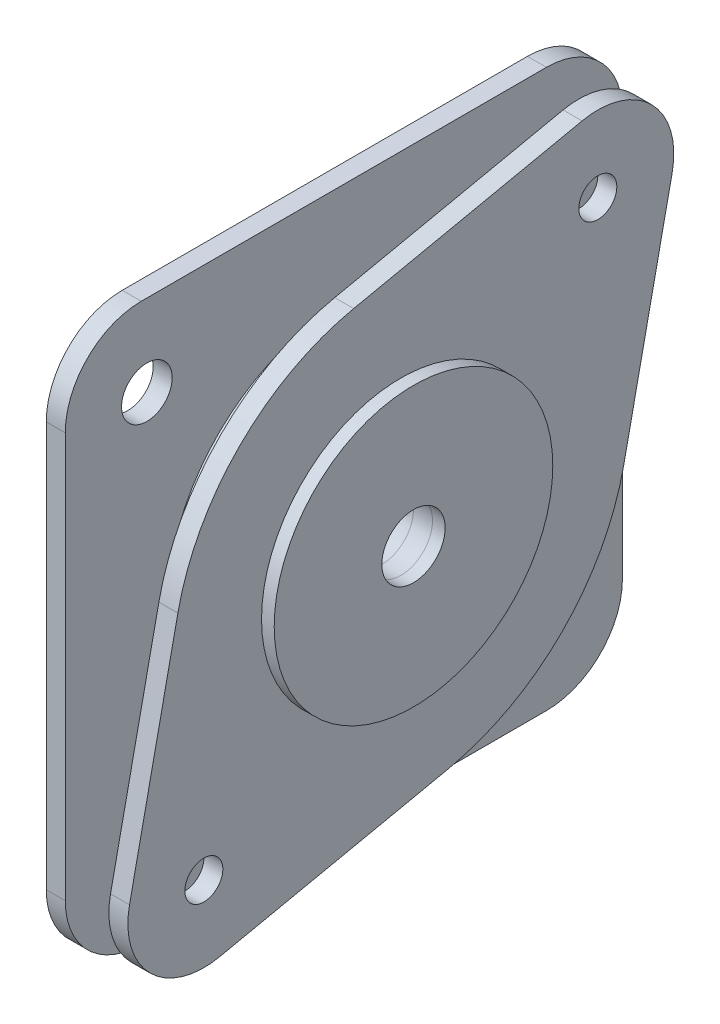
SolidWorks part; units mm, degrees
ref_plane "Front Plane" through (0, 0, 0) normal (0, 0, 1) x (1, 0, 0)
ref_plane "Top Plane" through (0, 0, 0) normal (0, 1, 0) x (1, 0, 0)
ref_plane "Right Plane" through (0, 0, 0) normal (1, 0, 0) x (0, 0, -1)
sketch "Sketch1" plane through (0, 0, 0) normal (1, 0, 0) x (0, 0, -1)
  line L0 (-16, 22) -> (16, 22)
  line L1 (-22, 16) -> (-22, -16)
  line L2 (-16, -22) -> (16, -22)
  line L3 (22, 16) -> (22, -16)
  arc A0 (-22, -16) -> (-16, -22) centre (-16, -16) ccw
  arc A1 (16, -22) -> (22, -16) centre (16, -16) ccw
  arc A2 (-16, 22) -> (-22, 16) centre (-16, 16) ccw
  arc A3 (16, 22) -> (22, 16) centre (16, 16) cw
  circle A4 centre (0, 0) radius 2.5
  point P4 (-22, 0)
  point P5 (0, 22)
  dimension "D1" = 6
  dimension "D2" = 44
extrude "Boss-Extrude1" add sketch "Sketch1" along normal blind 1.5
sketch "Sketch2" plane through (1.5, 0, 0) normal (1, 0, 0) x (0, 0, -1)
  circle A0 centre (0, 0) radius 2.5
  circle A1 centre (0, 0) radius 14
extrude "Boss-Extrude2" add sketch "Sketch2" along normal blind 3
sketch "Sketch3" plane through (4.5, 0, 0) normal (1, 0, 0) x (0, 0, -1)
  line L0 (0, 0) -> (15.5563, 15.5563) construction
  line L1 (0, 0) -> (0, 7.5568) construction
  circle A0 centre (15.5563, 15.5563) radius 2
  circle A1 centre (15.5563, -15.5563) radius 2
  circle A2 centre (-15.5563, -15.5563) radius 2
  circle A3 centre (-15.5563, 15.5563) radius 2
  point P13 (0, 0)
  dimension "D3" = 4
  dimension "D1" = 45
  dimension "D2" = 22
sketch "Sketch4" plane through (4.5, 0, 0) normal (1, 0, 0) x (0, 0, -1)
  line L0 (-3.7237, 17.6102) -> (14.3145, 21.4264)
  line L1 (17.6127, -3.7234) -> (21.4266, 14.3152)
  line L2 (-17.6079, 3.7269) -> (-21.4261, -14.3141)
  line L3 (3.727, -17.6104) -> (-14.3145, -21.4265)
  arc A0 (21.4266, 14.3152) -> (14.3145, 21.4264) centre (15.5563, 15.5563) ccw
  circle A1 centre (15.5563, 15.5563) radius 1.5
  arc A2 (-21.4261, -14.3141) -> (-14.3145, -21.4265) centre (-15.5561, -15.5564) ccw
  arc A4 (-3.7237, 17.6102) -> (-17.6079, 3.7269) centre (0.002, 0) ccw
  circle A5 centre (-15.5543, -15.5563) radius 1.5
  arc A6 (3.727, -17.6104) -> (17.6127, -3.7234) centre (0.002, 0) ccw
  circle A7 centre (0.002, 0) radius 2.502
  point P9 (0.0001, 0.0001)
  point P16 (0.001, 0)
  dimension "D1" = 2
  dimension "D2" = 2
extrude "Boss-Extrude3" add sketch "Sketch4" along normal blind 1.5
extrude "Cut-Extrude1" cut sketch "Sketch3" against normal blind 7.5
sketch "Sketch5" plane through (6, 0, 0) normal (1, 0, 0) x (0, 0, -1)
  circle A0 centre (0, 0) radius 11
  circle A1 centre (0, 0) radius 2.5
extrude "Boss-Extrude4" add sketch "Sketch5" along normal blind 1
